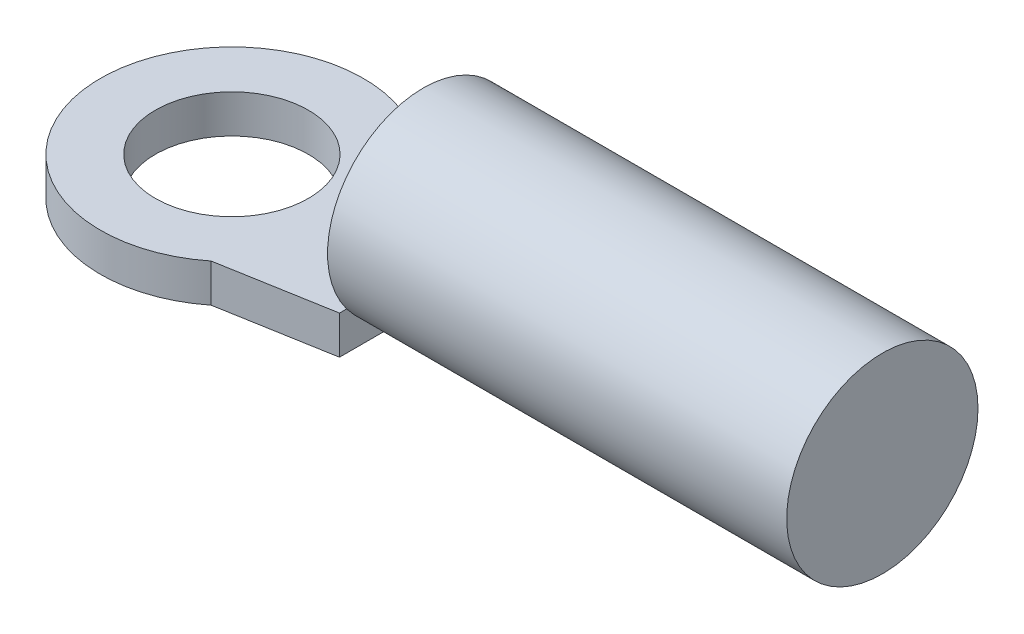
SolidWorks part; units mm, degrees
material "acero"
ref_plane "Alzado" through (0, 0, 0) normal (0, 0, 1) x (1, 0, 0)
ref_plane "Planta" through (0, 0, 0) normal (0, 1, 0) x (1, 0, 0)
ref_plane "Vista lateral" through (0, 0, 0) normal (1, 0, 0) x (0, 0, -1)
sketch "Sketch1" plane through (0, 0, 0) normal (0, 1, 0) x (1, 0, 0)
  line L0 (0, 0) -> (4, 0) construction
  line L1 (4, 1.75) -> (4, -1.75)
  line L2 (4, 1.75) -> (1.7146, 2.15)
  line L3 (4, -1.75) -> (1.7146, -2.15)
  circle A0 centre (0, 0) radius 1.6
  circle A1 centre (0, 0) radius 2.75
  point P7 (4, 0)
  dimension "D1" = 3.2
  dimension "D2" = 5.5
  dimension "D3" = 4
  dimension "D4" = 3.5
  dimension "D5" = 4.3
extrude "Boss-Extrude1" add sketch "Sketch1" along normal blind 0.8
sketch "Sketch2" plane through (4, 0, 0) normal (1, 0, 0) x (0, 0, -1)
  line L0 (0, 0) -> (0, 2) construction
  line L1 (1.75, 0) -> (-1.75, 0) construction
  circle A0 centre (0, 2) radius 2
  dimension "D1" = 4
extrude "Boss-Extrude2" add sketch "Sketch2" along normal blind 9.6
